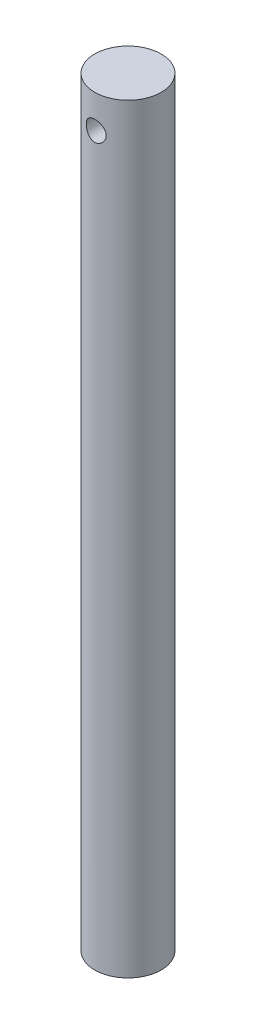
SolidWorks part; units mm, degrees
ref_plane "Front" through (0, 0, 0) normal (0, 0, 1) x (1, 0, 0)
ref_plane "Top" through (0, 0, 0) normal (0, 1, 0) x (1, 0, 0)
ref_plane "Right" through (0, 0, 0) normal (1, 0, 0) x (0, 0, -1)
sketch "Sketch1" plane through (0, 0, 0) normal (0, 1, 0) x (1, 0, 0)
  circle A0 centre (0, 0) radius 9.9949
  dimension "D1" = 19.9898
extrude "Boss-Extrude1" add sketch "Sketch1" along normal blind 228.6
sketch "Sketch2" plane through (0, 0, 0) normal (0, 0, 1) x (1, 0, 0)
  line L0 (9.9949, 228.6) -> (-9.9949, 228.6) construction
  circle A0 centre (0, 218.5924) radius 2.9972
  dimension "D1" = 10.0076
  dimension "D2" = 5.9944
extrude "Cut-Extrude1" cut sketch "Sketch2" against normal through all both and the other way through all contours A0
